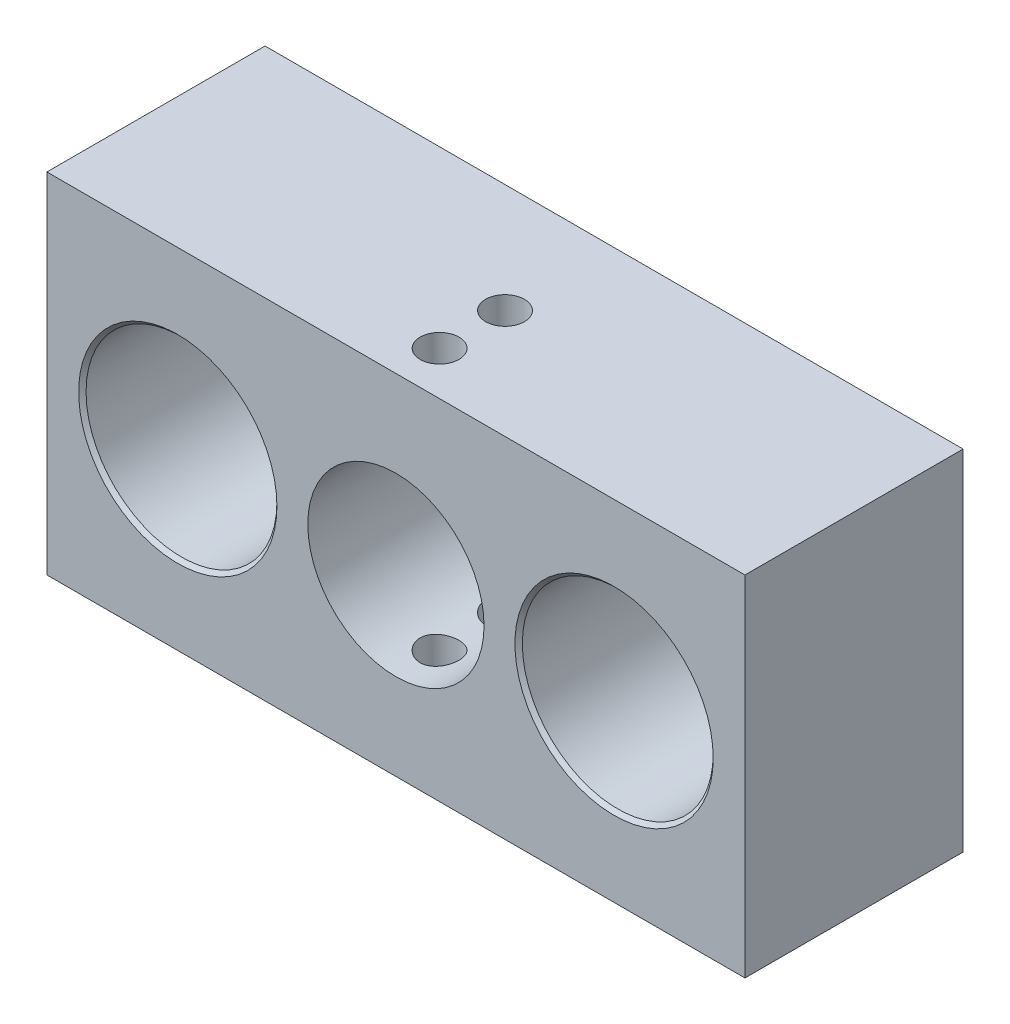
SolidWorks part; units mm, degrees
ref_plane "Front Plane" through (0, 0, 0) normal (0, 0, 1) x (1, 0, 0)
ref_plane "Top Plane" through (0, 0, 0) normal (0, 1, 0) x (1, 0, 0)
ref_plane "Right Plane" through (0, 0, 0) normal (1, 0, 0) x (0, 0, -1)
sketch "Sketch1" plane through (0, 0, 0) normal (0, 0, 1) x (1, 0, 0)
  line L1 (0, 0) -> (40.64, 0)
  line L2 (0, 0) -> (0, 20.32)
  line L3 (0, 20.32) -> (40.64, 20.32)
  line L4 (40.64, 0) -> (40.64, 20.32)
  dimension "D1" = 20.32
  dimension "D2" = 40.64
extrude "Boss-Extrude2" add sketch "Sketch1" along normal blind 12.7
hole_wizard "CBORE for 1/4 Socket Head Cap Screw1" positions "Sketch4" profile "Sketch3" counterbore size "1/4" standard "ANSI Inch" end condition through all
sketch "Sketch4" plane through (0, 0, 12.7) normal (0, 0, 1) x (1, 0, 0)
  line L0 (0, 20.32) -> (0, 0) construction
  line L1 (40.64, 0) -> (40.64, 20.32) construction
  line L2 (40.64, 20.32) -> (0, 20.32) construction
  point P0 (7.62, 10.16)
  point P2 (33.02, 10.16)
  dimension "D1" = 7.62
  dimension "D2" = 25.4
  dimension "D3" = 7.62
  dimension "D4" = 10.16
  dimension "D5" = 10.16
sketch "Sketch3" plane through (7.62, 10.16, 12.7) normal (1, 0, 0) x (0, -1, 0)
  line L0 (0, 0) -> (0, 12.7)
  line L1 (0, 12.7) -> (3.3782, 12.7)
  line L3 (3.3782, 12.7) -> (3.3782, 9.525)
  line L4 (5.5562, 9.525) -> (3.3782, 9.525)
  line L5 (5.5562, 9.525) -> (5.5562, 0.2159)
  line L6 (5.5562, 0.2159) -> (5.7721, 0)
  line L7 (5.7721, 0) -> (0, 0)
  line L8 (-5.5562, 0.2159) -> (-5.7721, 0) construction
  line L11 (0, -6.35) -> (0, 107.95) construction
  dimension "Thru Hole Dia." = 6.7564
  dimension "Thru Hole Depth" = 12.7
  dimension "C'Bore Dia." = 11.1125
  dimension "C'Bore Depth" = 9.525
  dimension "Near C'Sink Dia." = 11.5443
  dimension "Near C'Sink Angle" = 90
hole_wizard "Hole1" positions "Sketch7" profile "Sketch6" legacy
sketch "Sketch7" plane through (0, 0, 12.7) normal (0, 0, 1) x (1, 0, 0)
  line L0 (40.64, 20.32) -> (0, 20.32) construction
  line L1 (40.64, 0) -> (40.64, 20.32) construction
  point P0 (20.32, 10.16)
  dimension "D1" = 10.16
  dimension "D2" = 20.32
sketch "Sketch6" plane through (20.32, 10.16, 12.7) normal (1, 0, 0) x (0, -1, 0)
  line L0 (0, 0) -> (0, 9.525)
  line L1 (0, 9.525) -> (5.1308, 9.525)
  line L2 (5.1308, 9.525) -> (5.1308, 0)
  line L3 (5.1308, 0) -> (0, 0)
  line L4 (0, 110) -> (0, -10) construction
  dimension "Diameter" = 10.2616
  dimension "Depth" = 9.525
hole_wizard "#4-40 Tapped Hole1" positions "Sketch10" profile "Sketch8" tap size "#4-40" standard "ANSI Inch" end condition through all
sketch "Sketch10" plane through (0, 20.32, 0) normal (0, 1, 0) x (1, 0, 0)
  line L0 (0, -12.7) -> (0, 0) construction
  line L1 (40.64, -12.7) -> (0, -12.7) construction
  point P0 (20.32, -10.16)
  point P2 (20.32, -6.35)
  point P7 (20.32, -12.7)
  dimension "D1" = 20.32
  dimension "D2" = 20.32
  dimension "D3" = 2.54
  dimension "D4" = 3.81
sketch "Sketch8" plane through (20.32, 20.32, 10.16) normal (1, 0, 0) x (0, 0, 1)
  line L0 (0, 0) -> (0, 20.32)
  line L1 (0, 20.32) -> (1.1303, 20.32)
  line L2 (1.1303, 20.32) -> (1.1303, 0)
  line L5 (1.1303, 0) -> (0, 0)
  line L11 (0, -6.35) -> (0, 107.95) construction
  dimension "Thru Tap Drill Dia." = 2.2606
  dimension "Thru Tap Drill Depth" = 20.32
cosmetic thread "Hole Thread1" parameters "D2"=2.8448
cosmetic thread "Hole Thread2" parameters "D2"=2.8448
